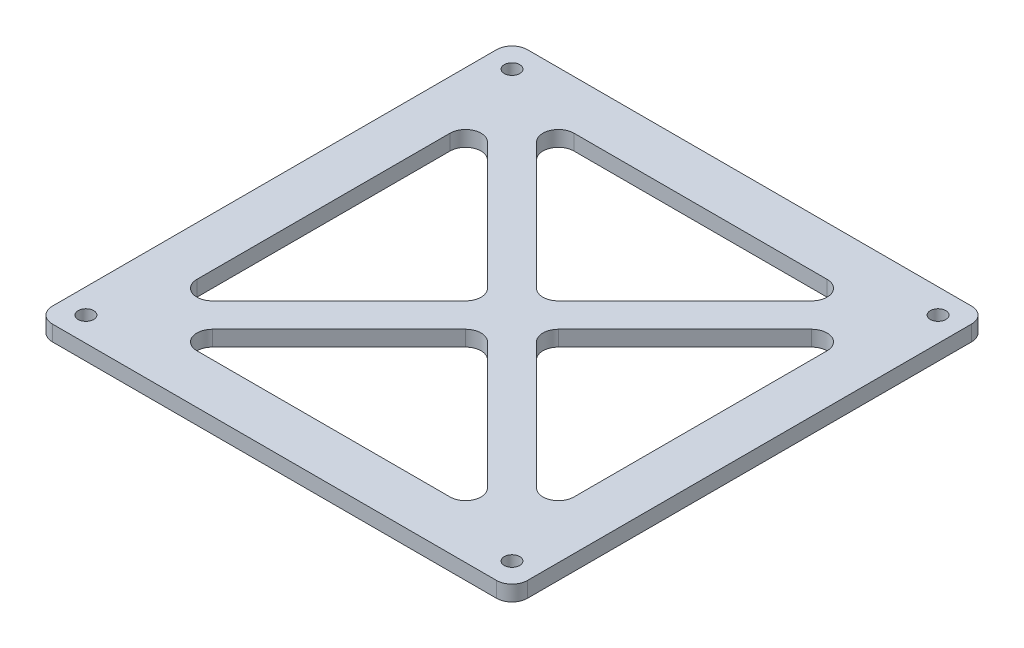
SolidWorks part; units mm, degrees
ref_plane "前基準面" through (0, 0, 0) normal (0, 0, 1) x (1, 0, 0)
ref_plane "上基準面" through (0, 0, 0) normal (0, 1, 0) x (1, 0, 0)
ref_plane "右基準面" through (0, 0, 0) normal (1, 0, 0) x (0, 0, -1)
ref_plane "平面1" through (0, 3, 0) normal (0, 1, 0) x (1, 0, 0)
sketch "草圖1" plane through (0, 3, 0) normal (0, 1, 0) x (1, 0, 0)
  line L0 (-46, 43) -> (-46, -43)
  line L1 (-43, -46) -> (43, -46)
  line L2 (46, -43) -> (46, 43)
  line L3 (43, 46) -> (-43, 46)
  line L4 (-31.3787, 26.6287) -> (-6.8713, 2.1213)
  line L5 (-6.8713, -2.1213) -> (-31.3787, -26.6287)
  line L6 (-36.5, -24.5074) -> (-36.5, 24.5074)
  line L7 (24.5074, -36.5) -> (-24.5074, -36.5)
  line L8 (-26.6287, -31.3787) -> (-2.1213, -6.8713)
  line L9 (2.1213, -6.8713) -> (26.6287, -31.3787)
  line L10 (-24.5074, 36.5) -> (24.5074, 36.5)
  line L11 (26.6287, 31.3787) -> (2.1213, 6.8713)
  line L12 (-2.1213, 6.8713) -> (-26.6287, 31.3787)
  line L13 (36.5, 24.5074) -> (36.5, -24.5074)
  line L14 (31.3787, -26.6287) -> (6.8713, -2.1213)
  line L15 (6.8713, 2.1213) -> (31.3787, 26.6287)
  arc A0 (-46, -43) -> (-43, -46) centre (-43, -43) ccw
  arc A1 (43, -46) -> (46, -43) centre (43, -43) ccw
  arc A2 (46, 43) -> (43, 46) centre (43, 43) ccw
  arc A3 (-43, 46) -> (-46, 43) centre (-43, 43) ccw
  circle A4 centre (41.25, -41.25) radius 1.5
  circle A5 centre (-41.25, 41.25) radius 1.5
  circle A6 centre (41.25, 41.25) radius 1.5
  circle A7 centre (-41.25, -41.25) radius 1.5
  arc A8 (-6.8713, 2.1213) -> (-6.8713, -2.1213) centre (-8.9926, 0) cw
  arc A9 (-31.3787, -26.6287) -> (-36.5, -24.5074) centre (-33.5, -24.5074) cw
  arc A10 (-36.5, 24.5074) -> (-31.3787, 26.6287) centre (-33.5, 24.5074) cw
  arc A11 (-24.5074, -36.5) -> (-26.6287, -31.3787) centre (-24.5074, -33.5) cw
  arc A12 (-2.1213, -6.8713) -> (2.1213, -6.8713) centre (0, -8.9926) cw
  arc A13 (26.6287, -31.3787) -> (24.5074, -36.5) centre (24.5074, -33.5) cw
  arc A14 (24.5074, 36.5) -> (26.6287, 31.3787) centre (24.5074, 33.5) cw
  arc A15 (2.1213, 6.8713) -> (-2.1213, 6.8713) centre (0, 8.9926) cw
  arc A16 (-26.6287, 31.3787) -> (-24.5074, 36.5) centre (-24.5074, 33.5) cw
  arc A17 (36.5, -24.5074) -> (31.3787, -26.6287) centre (33.5, -24.5074) cw
  arc A18 (6.8713, -2.1213) -> (6.8713, 2.1213) centre (8.9926, 0) cw
  arc A19 (31.3787, 26.6287) -> (36.5, 24.5074) centre (33.5, 24.5074) cw
extrude "填料-伸長1" add sketch "草圖1" against normal blind 3
